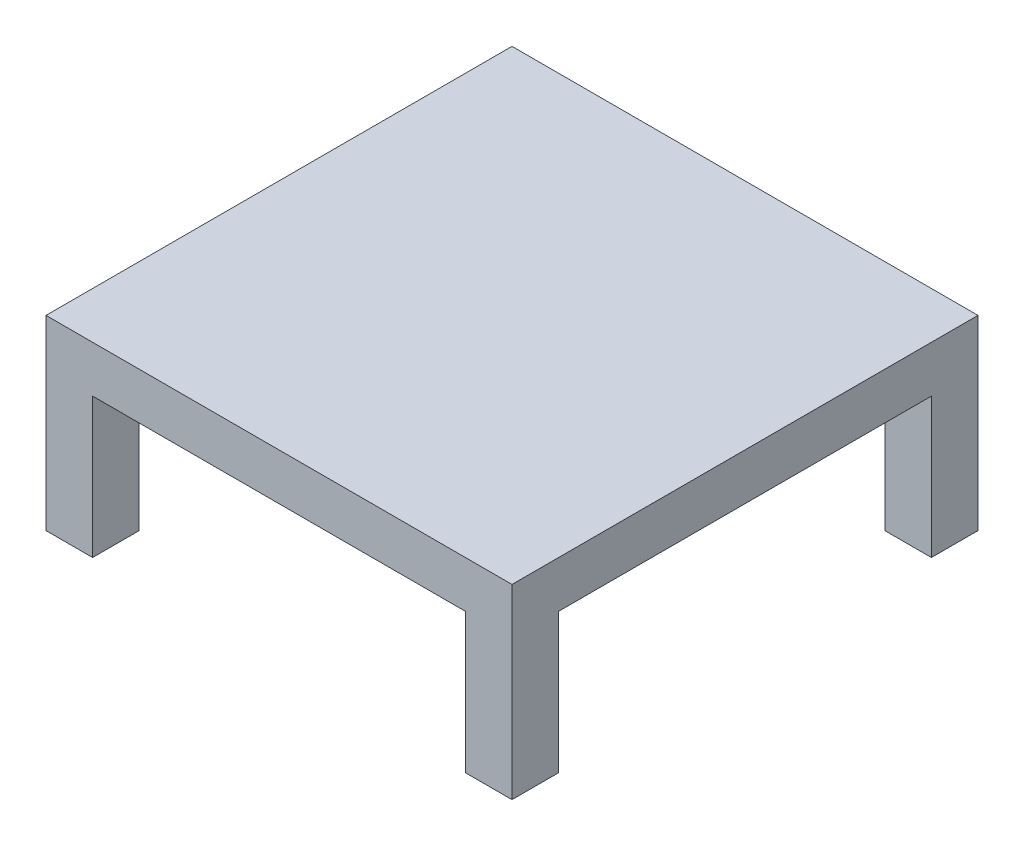
SolidWorks part; units mm, degrees
ref_plane "Front Plane" through (0, 0, 0) normal (0, 0, 1) x (1, 0, 0)
ref_plane "Top Plane" through (0, 0, 0) normal (0, 1, 0) x (1, 0, 0)
ref_plane "Right Plane" through (0, 0, 0) normal (1, 0, 0) x (0, 0, -1)
sketch "Sketch2" plane through (0, 0, 0) normal (0, 1, 0) x (1, 0, 0)
  line L1 (-50, 50) -> (50, 50)
  line L2 (-50, 50) -> (-50, -50)
  line L3 (-50, -50) -> (50, -50)
  line L4 (50, 50) -> (50, -50)
  line L5 (-50, 50) -> (50, -50) construction
  line L6 (-50, -50) -> (50, 50) construction
  point P0 (0, 0)
extrude "Boss-Extrude1" add sketch "Sketch2" along normal blind 10
sketch "Sketch3" plane through (0, 0, 0) normal (0, -1, 0) x (-1, 0, 0)
  line L1 (-50, -50) -> (-40, -50)
  line L2 (-50, -50) -> (-50, -40)
  line L3 (-50, -40) -> (-40, -40)
  line L4 (-40, -50) -> (-40, -40)
  line L5 (50, -50) -> (40, -50)
  line L6 (50, -50) -> (50, -40)
  line L7 (50, -40) -> (40, -40)
  line L8 (40, -50) -> (40, -40)
  line L9 (50, 50) -> (40, 50)
  line L10 (50, 50) -> (50, 40)
  line L11 (50, 40) -> (40, 40)
  line L12 (40, 50) -> (40, 40)
  line L13 (-50, 50) -> (-40, 50)
  line L14 (-50, 50) -> (-50, 40)
  line L15 (-50, 40) -> (-40, 40)
  line L16 (-40, 50) -> (-40, 40)
extrude "Boss-Extrude2" add sketch "Sketch3" along normal blind 30
